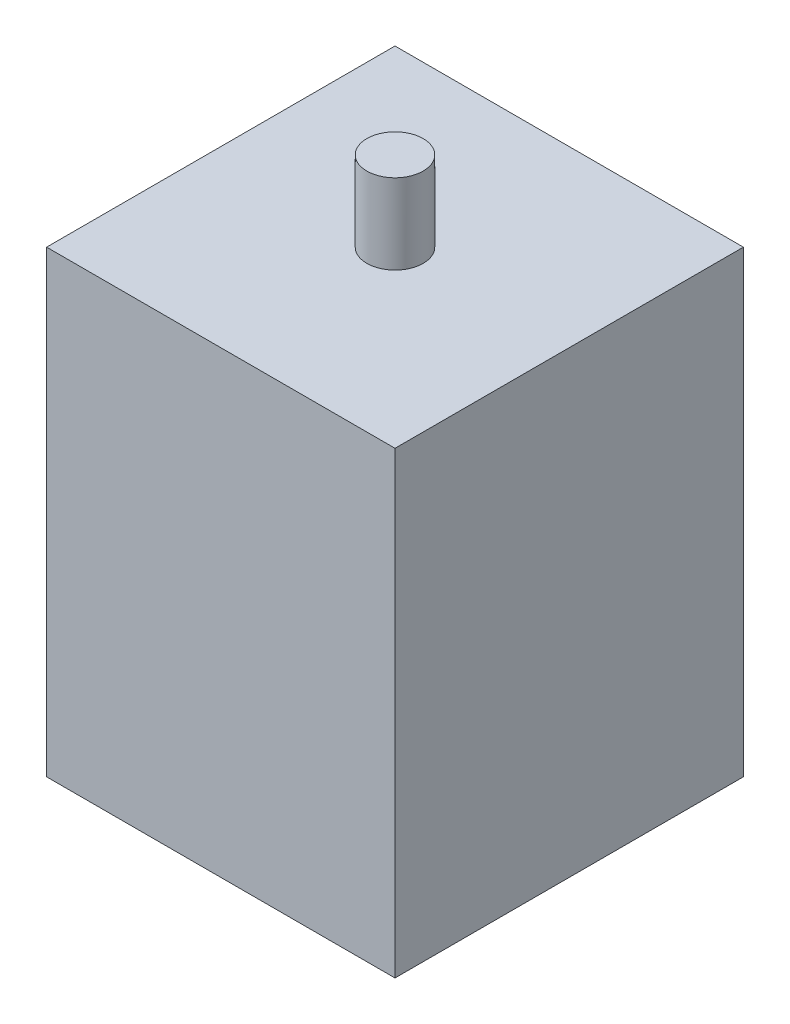
SolidWorks part; units mm, degrees
ref_plane "Front Plane" through (0, 0, 0) normal (0, 0, 1) x (1, 0, 0)
ref_plane "Top Plane" through (0, 0, 0) normal (0, 1, 0) x (1, 0, 0)
ref_plane "Right Plane" through (0, 0, 0) normal (1, 0, 0) x (0, 0, -1)
sketch "Sketch1" plane through (0, 0, 0) normal (0, 1, 0) x (1, 0, 0)
  line L1 (0, 0) -> (92.8, 0)
  line L2 (0, 0) -> (0, 92.8)
  line L3 (0, 92.8) -> (92.8, 92.8)
  line L4 (92.8, 0) -> (92.8, 92.8)
  dimension "D1" = 92.8
extrude "Boss-Extrude1" add sketch "Sketch1" along normal blind 122.2
sketch "Sketch2" plane through (0, 122.2, 0) normal (0, 1, 0) x (1, 0, 0)
  line L0 (46.4, 0) -> (46.4, 92.8) construction
  line L4 (0, 92.8) -> (0, 0)
  line L5 (0, 0) -> (92.8, 0)
  line L6 (92.8, 0) -> (92.8, 92.8)
  line L7 (92.8, 92.8) -> (0, 92.8)
  line L8 (0, 92.8) -> (0, 0)
  line L9 (0, 0) -> (92.8, 0)
  line L10 (92.8, 0) -> (92.8, 92.8)
  line L11 (92.8, 92.8) -> (0, 92.8)
  circle A0 centre (46.4, 46.4) radius 7.5
  dimension "D1" = 0
extrude "Boss-Extrude2" add sketch "Sketch2" along normal blind 21.3 contours A0
